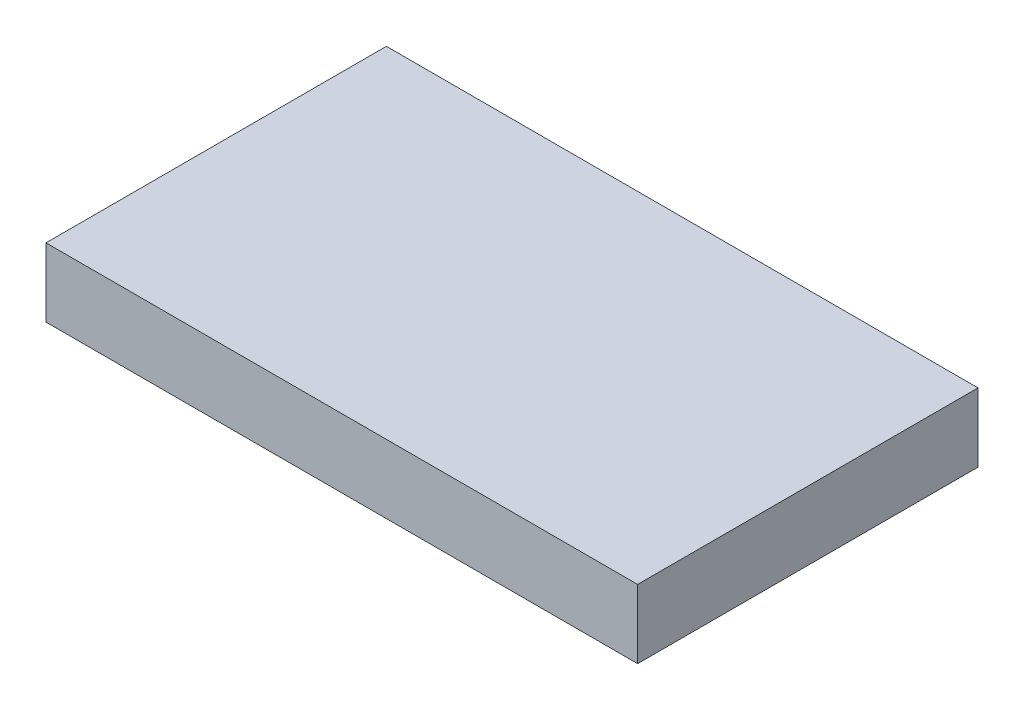
SolidWorks part; units mm, degrees
ref_plane "Front Plane" through (0, 0, 0) normal (0, 0, 1) x (1, 0, 0)
ref_plane "Top Plane" through (0, 0, 0) normal (0, 1, 0) x (1, 0, 0)
ref_plane "Right Plane" through (0, 0, 0) normal (1, 0, 0) x (0, 0, -1)
sketch "Sketch1" plane through (0, 0, 0) normal (0, 1, 0) x (1, 0, 0)
  line L1 (-49.5794, 42.2605) -> (36.5943, 42.2605)
  line L2 (-49.5794, 42.2605) -> (-49.5794, -7.3189)
  line L3 (-49.5794, -7.3189) -> (36.5943, -7.3189)
  line L4 (36.5943, 42.2605) -> (36.5943, -7.3189)
extrude "Boss-Extrude1" add sketch "Sketch1" along normal blind 10
